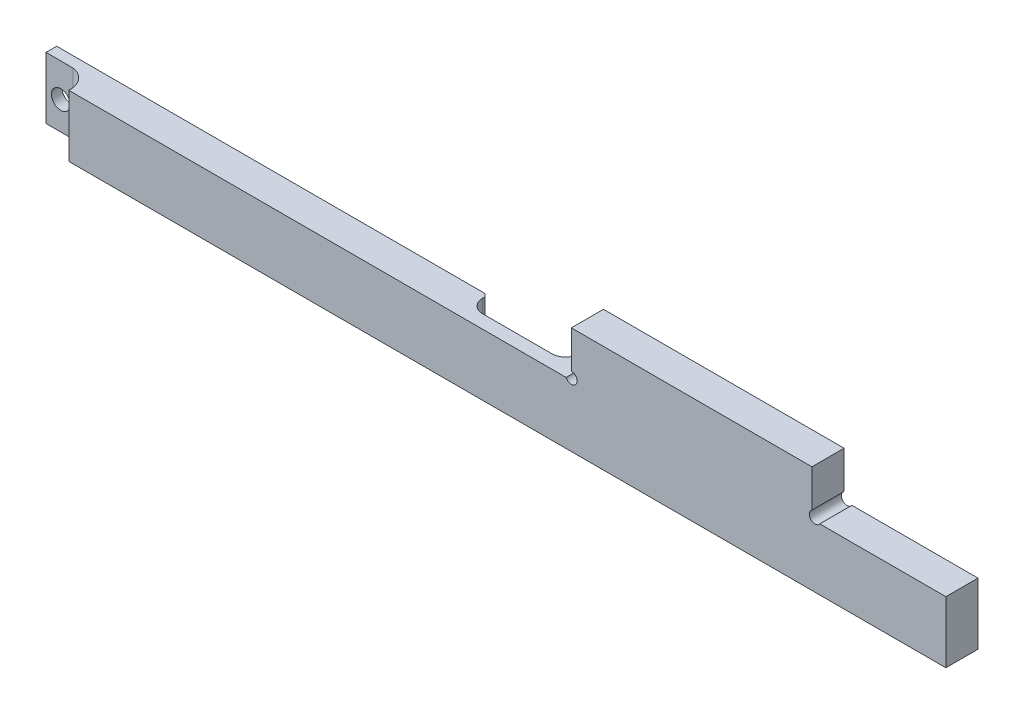
SolidWorks part; units mm, degrees
material "Pino"
ref_plane "Alzado" through (0, 0, 0) normal (0, 0, 1) x (1, 0, 0)
ref_plane "Planta" through (0, 0, 0) normal (0, 1, 0) x (1, 0, 0)
ref_plane "Vista lateral" through (0, 0, 0) normal (1, 0, 0) x (0, 0, -1)
sketch "Croquis1" plane through (0, 0, 0) normal (0, 0, 1) x (1, 0, 0)
  line L0 (216.337, 49.6273) -> (216.337, 26.6273)
  line L1 (-127.663, 49.6273) -> (74.5487, 49.6273)
  line L2 (-127.663, 49.6273) -> (-127.663, 26.6273)
  line L3 (-127.663, 26.6273) -> (216.337, 26.6273)
  line L5 (216.337, 49.6273) -> (216.337, -14.3727) construction
  line L6 (166.337, 52.6273) -> (166.337, 66.6273)
  line L7 (216.337, 66.6273) -> (166.337, 66.6273) construction
  line L8 (166.337, 66.6273) -> (76.487, 66.6273)
  line L9 (76.487, 52.6273) -> (76.487, 66.6273)
  line L10 (76.487, 52.6273) -> (76.487, 49.6273) construction
  line L11 (169.2545, 49.6273) -> (216.337, 49.6273)
  line L12 (74.5487, 49.6273) -> (76.487, 49.6273) construction
  line L13 (166.337, 52.6273) -> (166.337, 49.6273) construction
  line L14 (169.2545, 49.6273) -> (166.337, 49.6273) construction
  line L15 (166.337, 52.6273) -> (169.2545, 49.6273) construction
  line L16 (74.5487, 49.6273) -> (76.487, 52.6273) construction
  line L17 (166.337, 49.6273) -> (165.9403, 49.3229) construction
  arc A1 (76.487, 52.6273) -> (74.5487, 49.6273) centre (76.5079, 50.4875) cw
  arc A3 (166.337, 52.6273) -> (169.2545, 49.6273) centre (167.4744, 50.8147) ccw
  point P1 (166.337, 49.6273)
  point P14 (76.337, 49.6273)
  point P16 (165.9403, 49.3229)
  point P18 (0, 0)
  dimension "D4" = 89.85
  dimension "D5" = 50
  dimension "D9" = 0.5
  dimension "D2" = 23
  dimension "D3" = 17
  dimension "D6" = 344
  dimension "D11" = 4.1847
  dimension "D12" = 3.5717
extrude "Saliente-Extruir1" add sketch "Croquis1" along normal blind 12
sketch "Croquis3" plane through (0, 0, 0) normal (0, 0, -1) x (-1, 0, 0)
  line L7 (-33.337, 26.6273) -> (-33.337, 49.6273)
  line L8 (127.663, 26.6273) -> (-216.337, 26.6273) construction
  line L9 (-74.5487, 49.6273) -> (127.663, 49.6273) construction
  line L10 (127.663, 49.6273) -> (127.663, 26.6273) construction
  line L11 (-69.337, 26.6273) -> (-69.337, 49.6273)
  line L12 (-33.337, 26.6273) -> (-69.337, 26.6273)
  line L13 (-33.337, 49.6273) -> (-69.337, 49.6273)
  point P8 (-33.337, 38.1273)
  dimension "D1" = 161
  dimension "D2" = 36
extrude "Cortar-Extruir2" cut sketch "Croquis3" against normal blind 7
fillet "Redondeo1" radius 5 2 edges at (69.337, 38.1273, 7) (33.337, 38.1273, 7)
chamfer "Chaflán1" distance 1 angle 45 2 edges at (33.337, 38.1273, 0) (69.337, 38.1273, 0)
ref_plane "Plano1" through (0, 49.6273, 0) normal (0, 1, 0) x (1, 0, 0)
sketch "Croquis4" plane through (0, 49.6273, 0) normal (0, 1, 0) x (1, 0, 0)
  line L5 (-127.663, -12) -> (-127.663, -4)
  line L6 (-127.663, -12) -> (-127.663, 0) construction
  line L7 (-127.663, -4) -> (-117.663, -4)
  line L8 (-127.663, -12) -> (-111.163, -12)
  line L9 (74.5487, -12) -> (-127.663, -12) construction
  arc A3 (-117.663, -4) -> (-111.163, -12) centre (-118.6198, -11.4181) cw
  dimension "D4" = 7.4795
  dimension "D1" = 8
  dimension "D2" = 16.5
  dimension "D3" = 10
extrude "Cortar-Extruir3" cut sketch "Croquis4" against normal through all
ref_plane "Plano2" through (0, 0, 14) normal (0, 0, 1) x (1, 0, 0)
sketch "Croquis5" plane through (0, 0, 14) normal (0, 0, 1) x (1, 0, 0)
  line L0 (-122.163, 33.6273) -> (-122.163, 26.6273) construction
  line L2 (-117.663, 26.6273) -> (-127.663, 26.6273) construction
  line L3 (-125.663, 37.1273) -> (-127.663, 37.1273) construction
  line L5 (-127.663, 26.6273) -> (-127.663, 49.6273) construction
  circle A0 centre (-122.163, 37.1273) radius 3.5
  dimension "D1" = 7
  dimension "D2" = 7
  dimension "D3" = 2
extrude "Cortar-Extruir4" cut sketch "Croquis5" against normal blind 20
